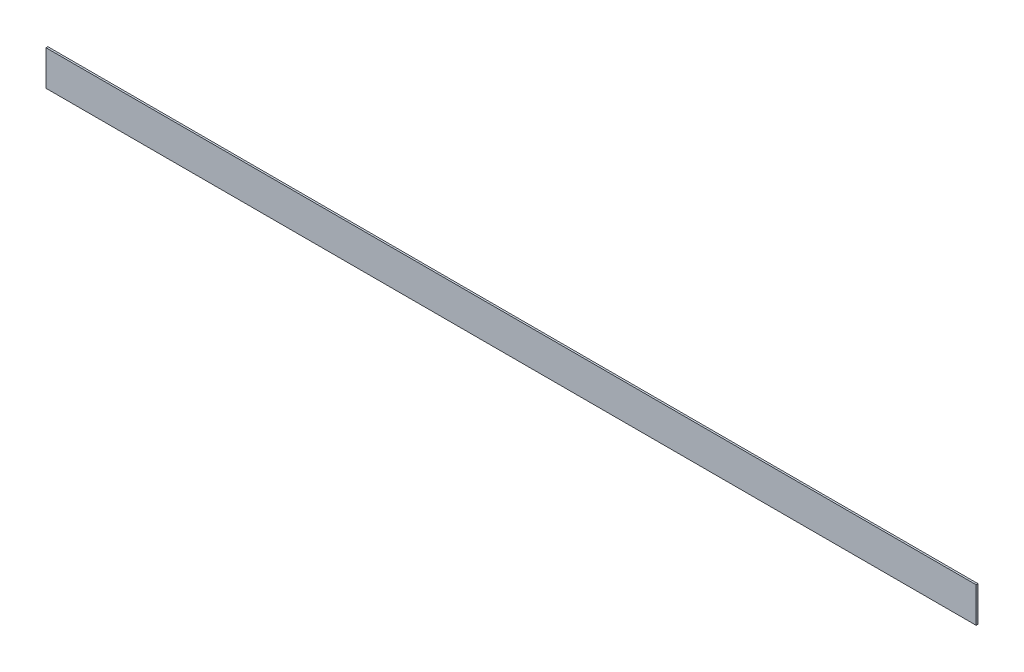
SolidWorks part; units mm, degrees
ref_plane "Front Plane" through (0, 0, 0) normal (0, 0, 1) x (1, 0, 0)
ref_plane "Top Plane" through (0, 0, 0) normal (0, 1, 0) x (1, 0, 0)
ref_plane "Right Plane" through (0, 0, 0) normal (1, 0, 0) x (0, 0, -1)
sketch "Sketch1" plane through (0, 0, 0) normal (0, 0, 1) x (1, 0, 0)
  line L1 (0, 0) -> (12700, 0)
  line L2 (0, 0) -> (0, -480)
  line L3 (0, -480) -> (12700, -480)
  line L4 (12700, 0) -> (12700, -480)
  dimension "D1" = 480
  dimension "D2" = 12700
extrude "Boss-Extrude1" add sketch "Sketch1" along normal blind 25.4
